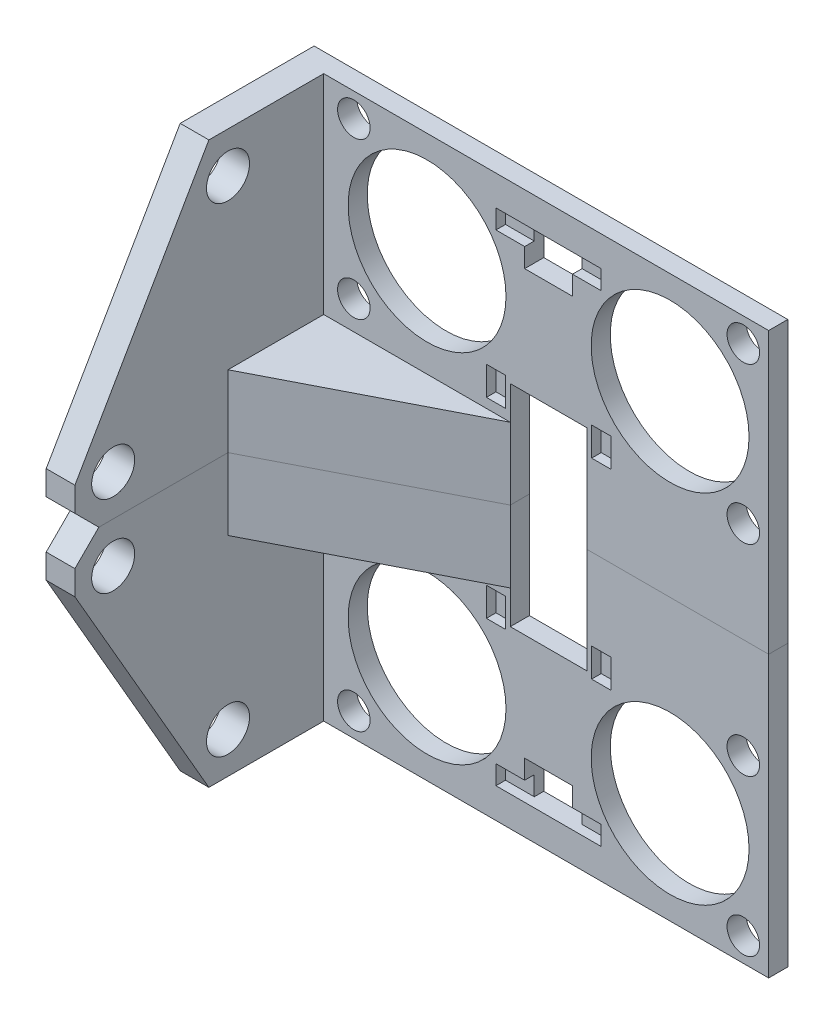
SolidWorks part; units mm, degrees
ref_plane "前基準面" through (0, 0, 0) normal (0, 0, 1) x (1, 0, 0)
ref_plane "上基準面" through (0, 0, 0) normal (0, 1, 0) x (1, 0, 0)
ref_plane "右基準面" through (0, 0, 0) normal (1, 0, 0) x (0, 0, -1)
sketch "草圖1" plane through (0, 0, 0) normal (0, 0, 1) x (1, 0, 0)
  line L1 (-23, -10.65) -> (23, -10.65)
  line L2 (-23, -10.65) -> (-23, 10.65)
  line L3 (-23, 10.65) -> (23, 10.65)
  line L4 (23, -10.65) -> (23, 10.65)
  line L5 (-23, -10.65) -> (23, 10.65) construction
  line L6 (-23, 10.65) -> (23, -10.65) construction
  point P0 (0, 0)
  dimension "D1" = 46
  dimension "D2" = 21.3
extrude "填料-伸長1" add sketch "草圖1" along normal blind 2
sketch "草圖2" plane through (0, 0, 2) normal (0, 0, 1) x (1, 0, 0)
  line L0 (-12.7, 0) -> (12.7, 0) construction
  circle A0 centre (-12.7, 0) radius 8.25
  circle A1 centre (12.7, 0) radius 8.25
  point P4 (0, 0)
  dimension "D1" = 25.4
  dimension "D2" = 16.5
extrude "除料-伸長1" cut sketch "草圖2" against normal through all
sketch "草圖3" plane through (0, 0, 2) normal (0, 0, 1) x (1, 0, 0)
  line L0 (0, 0) -> (0, 9.15) construction
  line L1 (23, 10.65) -> (-23, 10.65) construction
  line L2 (-4, 7.65) -> (4, 7.65)
  line L3 (-4, 7.65) -> (-4, 10.65)
  line L4 (-4, 10.65) -> (4, 10.65)
  line L5 (4, 7.65) -> (4, 10.65)
  line L6 (-4, 7.65) -> (4, 10.65) construction
  line L7 (-4, 10.65) -> (4, 7.65) construction
  dimension "D1" = 8
  dimension "D2" = 3
extrude "除料-伸長2" cut sketch "草圖3" against normal through all
sketch "草圖4" plane through (0, 0, 2) normal (0, 0, 1) x (1, 0, 0)
  line L0 (0, 0) -> (0, -5.5) construction
  line L2 (-2.5, -3.5) -> (2.5, -3.5)
  line L3 (-2.5, -3.5) -> (-2.5, -7.5)
  line L4 (-2.5, -7.5) -> (2.5, -7.5)
  line L5 (2.5, -3.5) -> (2.5, -7.5)
  line L6 (-2.5, -3.5) -> (2.5, -7.5) construction
  line L7 (-2.5, -7.5) -> (2.5, -3.5) construction
  dimension "D1" = 5
  dimension "D2" = 4
  dimension "D3" = 5.5
extrude "除料-伸長3" cut sketch "草圖4" against normal through all
sketch "草圖5" plane through (0, 0, 2) normal (0, 0, 1) x (1, 0, 0)
  line L0 (0, 0) -> (0, 8.65) construction
  line L1 (2.5, -7.5) -> (5.5, -7.5)
  line L2 (2.5, -7.5) -> (2.5, -5.5)
  line L3 (2.5, -5.5) -> (5.5, -5.5)
  line L4 (5.5, -7.5) -> (5.5, -5.5)
  line L5 (-5.5, 8.65) -> (5.5, 8.65) construction
  line L6 (23, 10.65) -> (4, 10.65) construction
  line L7 (-4.5, 10.15) -> (-6.5, 10.15)
  line L8 (-4.5, 10.15) -> (-4.5, 7.15)
  line L9 (-4.5, 7.15) -> (-6.5, 7.15)
  line L10 (-6.5, 10.15) -> (-6.5, 7.15)
  line L11 (-4.5, 10.15) -> (-6.5, 7.15) construction
  line L12 (-4.5, 7.15) -> (-6.5, 10.15) construction
  line L13 (6.5, 10.15) -> (4.5, 10.15)
  line L14 (6.5, 10.15) -> (6.5, 7.15)
  line L15 (6.5, 7.15) -> (4.5, 7.15)
  line L16 (4.5, 10.15) -> (4.5, 7.15)
  line L17 (6.5, 10.15) -> (4.5, 7.15) construction
  line L18 (6.5, 7.15) -> (4.5, 10.15) construction
  line L20 (-2.5, -7.5) -> (-5.5, -7.5)
  line L21 (-2.5, -7.5) -> (-2.5, -5.5)
  line L22 (-2.5, -5.5) -> (-5.5, -5.5)
  line L23 (-5.5, -7.5) -> (-5.5, -5.5)
  point P10 (0, 8.65)
  dimension "D1" = 2
  dimension "D2" = 3
  dimension "D3" = 2
  dimension "D4" = 3
  dimension "D5" = 11
  dimension "D6" = 0.5
extrude "除料-伸長4" cut sketch "草圖5" against normal blind 1
hole_wizard "M3 餘隙孔1" positions "草圖6" profile "草圖7" hole size "M3" standard "Ansi Metric" end condition through all
sketch "草圖6" plane through (0, 0, 2) normal (0, 0, 1) x (1, 0, 0)
  line L1 (-20.35, -8.15) -> (20.35, -8.15) construction
  line L2 (-20.35, -8.15) -> (-20.35, 8.15) construction
  line L3 (-20.35, 8.15) -> (20.35, 8.15) construction
  line L4 (20.35, -8.15) -> (20.35, 8.15) construction
  line L5 (-20.35, -8.15) -> (20.35, 8.15) construction
  line L6 (-20.35, 8.15) -> (20.35, -8.15) construction
  point P1 (20.35, 8.15)
  point P112 (-20.35, -8.15)
  point P113 (-20.35, 8.15)
  point P114 (20.35, -8.15)
  dimension "D1" = 16.3
  dimension "D2" = 40.7
sketch "草圖7" plane through (20.35, 8.15, 2) normal (1, 0, 0) x (0, -1, 0)
  line L0 (0, 0) -> (0, 2)
  line L1 (0, 2) -> (1.7, 2)
  line L2 (1.7, 2) -> (1.7, 0)
  line L5 (1.7, 0) -> (0, 0)
  line L11 (0, -6.35) -> (0, 107.95) construction
  dimension "貫穿孔直徑" = 3.4
  dimension "貫穿孔深度" = 2
sketch "草圖9" plane through (0, 10.65, 0) normal (0, 1, 0) x (1, 0, 0)
  line L1 (23, -2) -> (-23, -2)
  line L2 (23, -2) -> (23, 0)
  line L3 (23, 0) -> (-23, 0)
  line L4 (-23, -2) -> (-23, 0)
extrude "填料-伸長3" add sketch "草圖9" along normal blind 8
sketch "草圖10" plane through (0, 0, 2) normal (0, 0, 1) x (1, 0, 0)
  line L0 (-23, 18.65) -> (23, 18.65) construction
  line L1 (-4, 10.65) -> (4, 10.65)
  line L2 (-4, 10.65) -> (-4, 18.65)
  line L3 (-4, 18.65) -> (4, 18.65)
  line L4 (4, 10.65) -> (4, 18.65)
extrude "除料-伸長5" cut sketch "草圖10" against normal through all
sketch "草圖11" plane through (-23, 0, 0) normal (-1, 0, 0) x (0, 0, 1)
  line L1 (2, 18.65) -> (0, 18.65)
  line L2 (2, 18.65) -> (2, -10.65)
  line L3 (2, -10.65) -> (0, -10.65)
  line L4 (0, 18.65) -> (0, -10.65)
extrude "填料-伸長4" add sketch "草圖11" along normal blind 0.5
sketch "草圖12" plane through (0, 0, 0) normal (0, 0, 1) x (1, 0, 0)
  line L1 (-23.5, -10.65) -> (-26.5, -10.65)
  line L2 (-23.5, -10.65) -> (-23.5, 18.65)
  line L3 (-23.5, 18.65) -> (-26.5, 18.65)
  line L4 (-26.5, -10.65) -> (-26.5, 18.65)
  dimension "D1" = 3
extrude "填料-伸長5" add sketch "草圖12" along normal blind 28
hole_wizard "M4 餘隙孔1" positions "草圖13" profile "草圖14" hole size "M4" standard "Ansi Metric" end condition through all
sketch "草圖13" plane through (-23.5, 0, 0) normal (1, 0, 0) x (0, 0, -1)
  line L0 (-24, 14.3923) -> (-12, -6.3923) construction
  line L3 (-2, -10.65) -> (-2, 18.65) construction
  line L10 (-18, 4) -> (-28, 4) construction
  line L11 (-28, -10.65) -> (-28, 18.65) construction
  point P0 (-24, 14.3923)
  point P1 (-12, -6.3923)
  dimension "D1" = 30
  dimension "D2" = 24
  dimension "D3" = 10
sketch "草圖14" plane through (-23.5, 14.3923, 24) normal (0, 1, 0) x (0, 0, -1)
  line L0 (0, 0) -> (0, 3)
  line L1 (0, 3) -> (2.25, 3)
  line L2 (2.25, 3) -> (2.25, 0)
  line L5 (2.25, 0) -> (0, 0)
  line L11 (0, -6.35) -> (0, 107.95) construction
  dimension "貫穿孔直徑" = 4.5
  dimension "貫穿孔深度" = 3
chamfer "導角1" distance 14 angle 60 1 edges at (-25, -10.65, 28)
chamfer "導角2" distance 2.5 angle 45 1 edges at (-25, 18.65, 28)
sketch "草圖16" plane through (0, 18.65, 0) normal (0, 1, 0) x (1, 0, 0)
  line L0 (-23.5, -12) -> (-4, -2)
  line L1 (-23.5, -25.5) -> (-23.5, -2) construction
  line L2 (-23.5, -2) -> (-4, -2) construction
  dimension "D1" = 10
rib "肋材1" sketch "草圖16" sketch "草圖16" thickness 7.5 extrusion direction parallel to sketch draft on no parameters "D1"=7.5
ref_plane "平面1" through (0, 18.65, 0) normal (0, 1, 0) x (1, 0, 0)
mirror "鏡射1" about plane through (0, 18.65, 0) normal (0, 1, 0) of bodies 112
split "分割1" trim tools "平面1" bodies to split 112 114 resulting bodies 115 116
